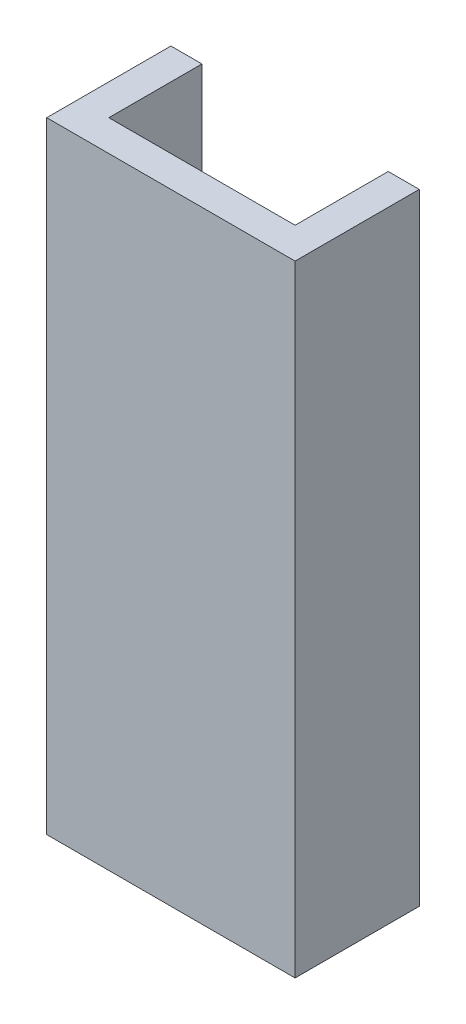
SolidWorks part; units mm, degrees
ref_plane "Front Plane" through (0, 0, 0) normal (0, 0, 1) x (1, 0, 0)
ref_plane "Top Plane" through (0, 0, 0) normal (0, 1, 0) x (1, 0, 0)
ref_plane "Right Plane" through (0, 0, 0) normal (1, 0, 0) x (0, 0, -1)
sketch "Sketch1" plane through (0, 0, 0) normal (0, 1, 0) x (1, 0, 0)
  line L0 (-20, 0) -> (20, 0)
  line L1 (20, 0) -> (20, 20)
  line L2 (20, 20) -> (15, 20)
  line L3 (15, 20) -> (15, 5)
  line L4 (15, 5) -> (-15, 5)
  line L5 (0, 0) -> (0, 26.2289) construction
  line L6 (-15, 20) -> (-15, 5)
  line L7 (-20, 20) -> (-15, 20)
  line L8 (-20, 0) -> (-20, 20)
  point P9 (0, 5)
  dimension "D1" = 20
  dimension "D2" = 5
  dimension "D3" = 5
  dimension "D5" = 20
extrude "Boss-Extrude1" add sketch "Sketch1" along normal blind 100
